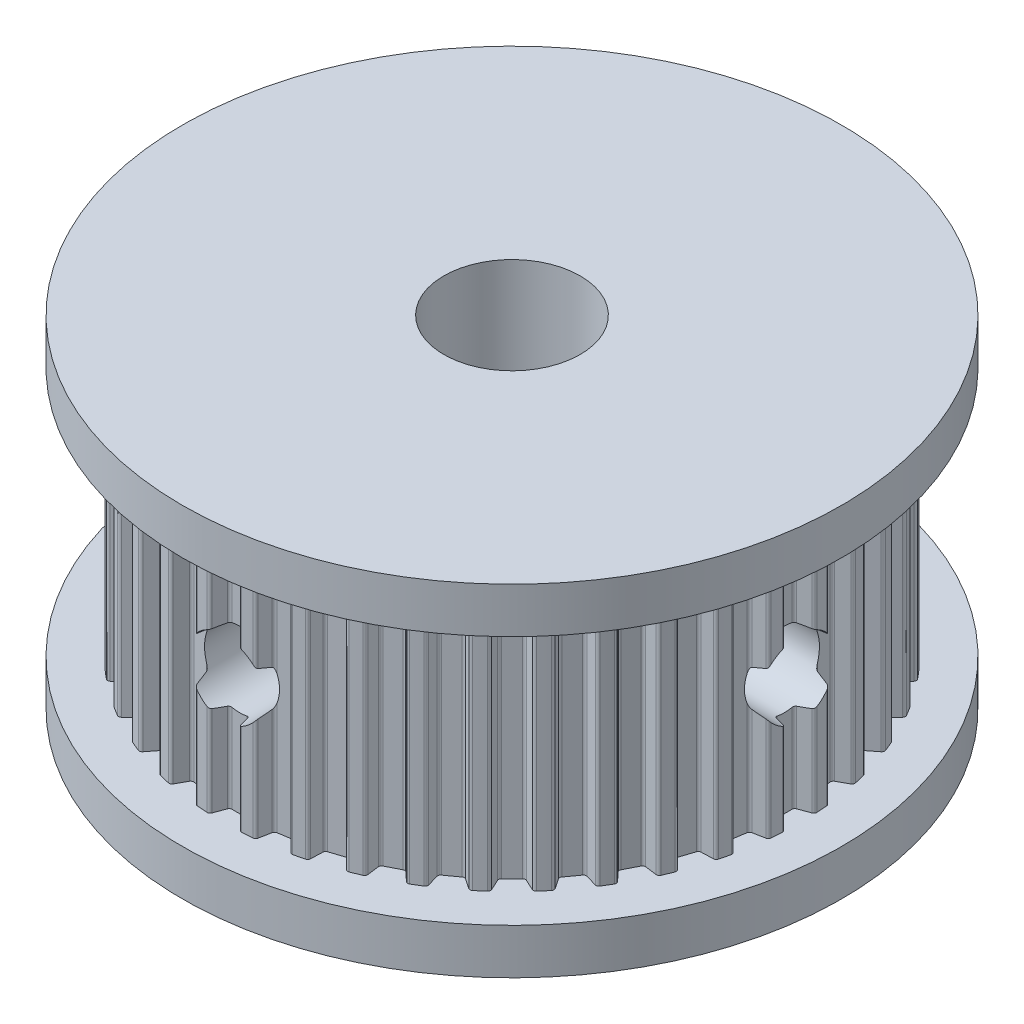
SolidWorks part; units mm, degrees
ref_plane "Front Plane" through (0, 0, 0) normal (0, 0, 1) x (1, 0, 0)
ref_plane "Top Plane" through (0, 0, 0) normal (0, 1, 0) x (1, 0, 0)
ref_plane "Right Plane" through (0, 0, 0) normal (1, 0, 0) x (0, 0, -1)
sketch "草圖1" plane through (0, 0, 0) normal (0, 1, 0) x (1, 0, 0)
  circle A0 centre (0, 0) radius 12.68
  dimension "D1" = 25.36
extrude "填料-伸長1" add sketch "草圖1" along normal mid plane 11 contours A0
sketch "草圖2" plane through (0, -5.5, 0) normal (0, -1, 0) x (1, 0, 0)
  line L0 (0, 12.68) -> (0, 0) construction
  line L1 (0, 11.99) -> (-0.42, 11.99)
  line L2 (-0.42, 11.99) -> (-0.6648, 12.6626)
  line L3 (0, 11.99) -> (0.42, 11.99)
  line L4 (0.42, 11.99) -> (0.6648, 12.6626)
  circle A0 centre (0, 0) radius 12.68 construction
  arc A1 (-0.6648, 12.6626) -> (0.6648, 12.6626) centre (0, 0) cw
  circle M7 centre (0, 0) radius 12.68
  dimension "D1" = 0.69
  dimension "D2" = 0.84
  dimension "D3" = 40
extrude "除料-伸長1" cut sketch "草圖2" against normal through all contours L0 A1 L2 L1 | L0 L3 L4 M7
fillet "圓角1" radius 0.13 4 edges at (-0.6648, 0, 12.6626) (0.6648, 0, 12.6626) (0.42, 0, 11.99) (-0.42, 0, 11.99)
pattern_circular "環狀複製排列1" count 40 over 360 about axis through (0, 0, 0) along (0, 1, 0) of "圓角1", "除料-伸長1"
sketch "草圖3" plane through (0, 5.5, 0) normal (0, 1, 0) x (1, 0, 0)
  circle A0 centre (0, 0) radius 14.5
  dimension "D1" = 29
extrude "填料-伸長2" add sketch "草圖3" along normal blind 2
sketch "草圖4" plane through (0, -5.5, 0) normal (0, -1, 0) x (1, 0, 0)
  circle A0 centre (0, 0) radius 14.5
  circle A1 centre (0, 0) radius 14.5 construction
extrude "填料-伸長3" add sketch "草圖4" along normal blind 2
sketch "草圖5" plane through (0, -7.5, 0) normal (0, -1, 0) x (1, 0, 0)
  circle A0 centre (0, 0) radius 3
  dimension "D1" = 6
extrude "除料-伸長2" cut sketch "草圖5" against normal through all
hole_wizard "M4x0.7 螺紋孔1" positions "草圖8" profile "草圖9" tap size "M4x0.7" standard "Ansi Metric"
sketch "草圖8" plane through (0, 0, 0) normal (0, 0, 1) x (1, 0, 0)
  point P5 (0, 0)
  point P15 (0, 0)
  point P16 (0, 0)
  point P17 (0, 0)
sketch "草圖9" plane through (0, 0, 0) normal (1, 0, 0) x (0, 1, 0)
  line L0 (0, 0) -> (0, 14.5)
  line L1 (0, 14.5) -> (1.65, 14.5)
  line L2 (1.65, 14.5) -> (1.65, 0)
  line L5 (1.65, 0) -> (0, 0)
  line L11 (0, -6.35) -> (0, 107.95) construction
  dimension "貫穿螺孔鑽直徑" = 3.3
  dimension "貫穿螺孔鑽深度" = 14.5
pattern_circular "環狀複製排列2" count 2 over 90 about axis through (0, 7.5, 0) along (0, -1, 0) of "M4x0.7 螺紋孔1"
